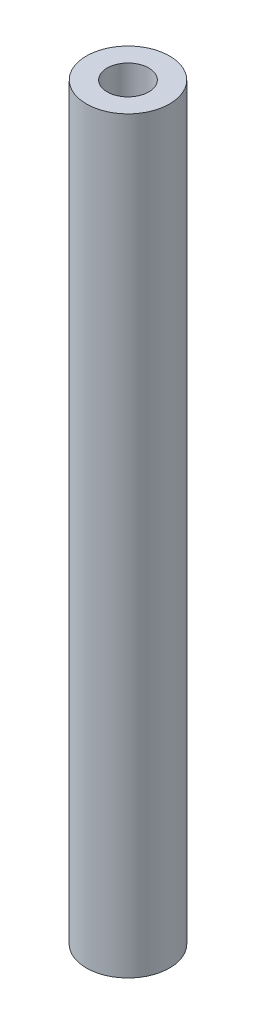
SolidWorks part; units mm, degrees
material "6061-T6 (SS)"
ref_plane "Front Plane" through (0, 0, 0) normal (0, 0, 1) x (1, 0, 0)
ref_plane "Top Plane" through (0, 0, 0) normal (0, 1, 0) x (1, 0, 0)
ref_plane "Right Plane" through (0, 0, 0) normal (1, 0, 0) x (0, 0, -1)
sketch "Sketch1" plane through (0, 0, 0) normal (0, 1, 0) x (1, 0, 0)
  circle A0 centre (0, 0) radius 2.5
  circle A1 centre (0, 0) radius 5
  dimension "D1" = 5
  dimension "D2" = 10
extrude "Boss-Extrude1" add sketch "Sketch1" along normal blind 90
